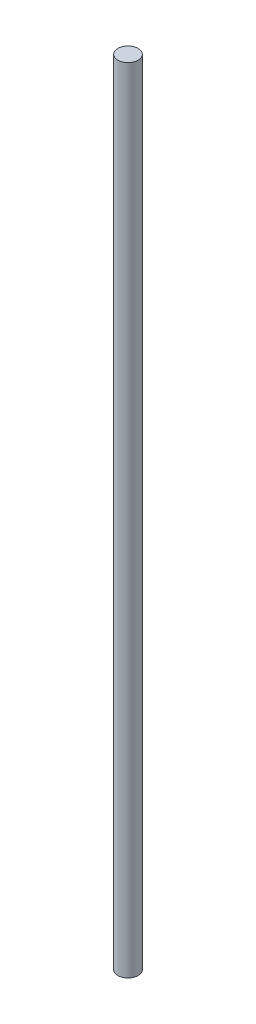
SolidWorks part; units mm, degrees
ref_plane "Front Plane" through (0, 0, 0) normal (0, 0, 1) x (1, 0, 0)
ref_plane "Top Plane" through (0, 0, 0) normal (0, 1, 0) x (1, 0, 0)
ref_plane "Right Plane" through (0, 0, 0) normal (1, 0, 0) x (0, 0, -1)
sketch "Sketch1" plane through (0, 0, 0) normal (0, 1, 0) x (1, 0, 0)
  circle A0 centre (0, 0) radius 3.175
  dimension "D1" = 6.35
extrude "Boss-Extrude1" add sketch "Sketch1" along normal blind 247.65
